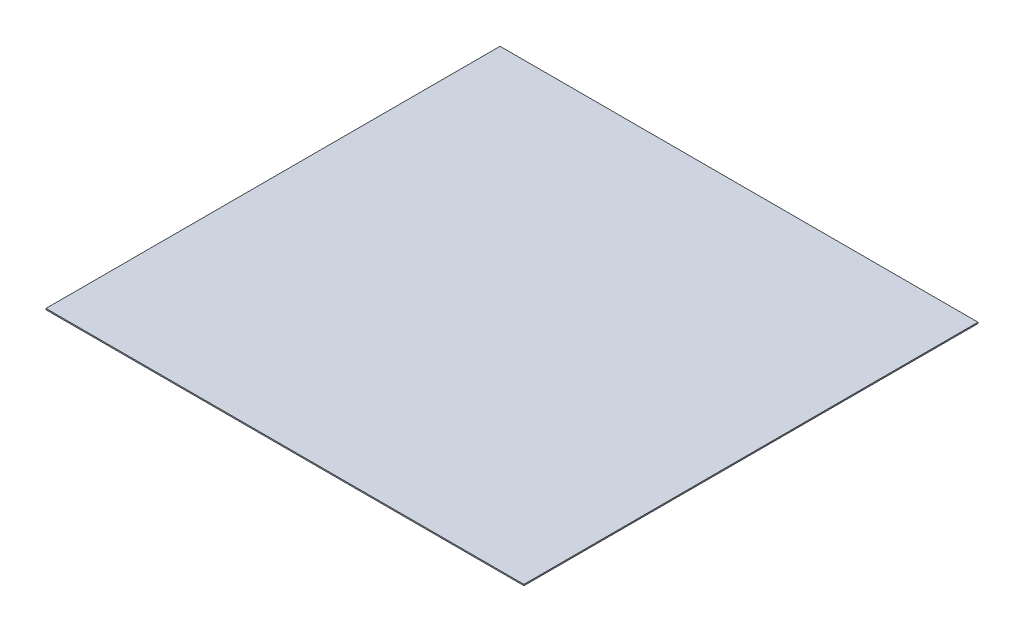
SolidWorks part; units mm, degrees
ref_plane "Płaszczyzna przednia" through (0, 0, 0) normal (0, 0, 1) x (1, 0, 0)
ref_plane "Płaszczyzna górna" through (0, 0, 0) normal (0, 1, 0) x (1, 0, 0)
ref_plane "Płaszczyzna prawa" through (0, 0, 0) normal (1, 0, 0) x (0, 0, -1)
sketch "Szkic1" plane through (0, 0, 0) normal (0, 1, 0) x (1, 0, 0)
  line L1 (-597.5371, -363.7915) -> (202.4629, -363.7915)
  line L2 (-597.5371, -363.7915) -> (-597.5371, 396.2085)
  line L3 (-597.5371, 396.2085) -> (202.4629, 396.2085)
  line L4 (202.4629, -363.7915) -> (202.4629, 396.2085)
  dimension "D1" = 760
  dimension "D2" = 800
extrude "Dodanie-wyciągnięcie1" add sketch "Szkic1" along normal blind 2
